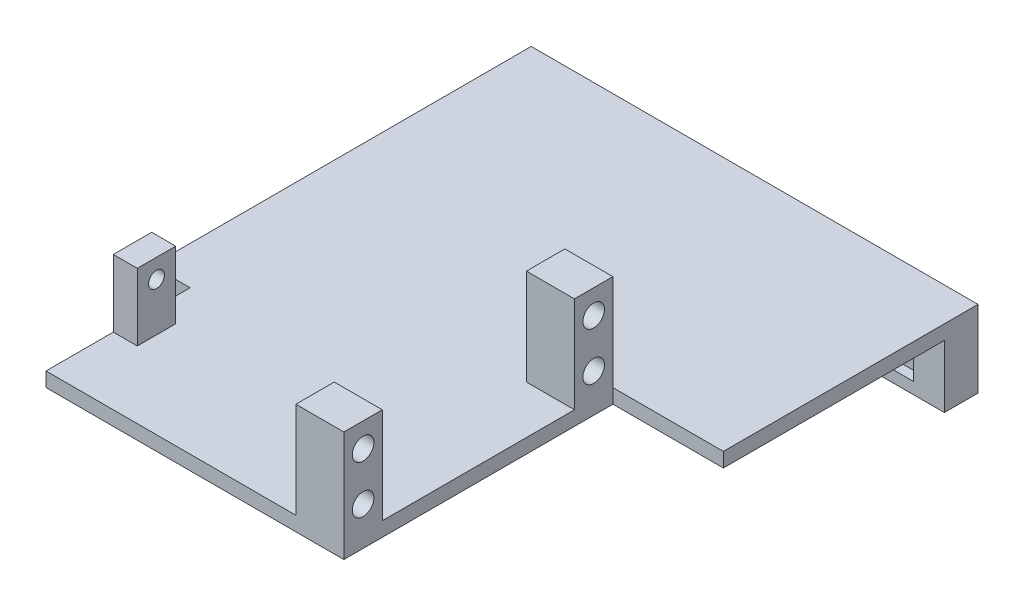
SolidWorks part; units mm, degrees
ref_plane "Plan de face" through (0, 0, 0) normal (0, 0, 1) x (1, 0, 0)
ref_plane "Plan de dessus" through (0, 0, 0) normal (0, 1, 0) x (1, 0, 0)
ref_plane "Plan de droite" through (0, 0, 0) normal (1, 0, 0) x (0, 0, -1)
sketch "Esquisse2" plane through (0, 0, 0) normal (1, 0, 0) x (0, 0, -1)
  line L0 (-24, 10) -> (-24, -10) construction
  line L1 (-24, 5) -> (24, 5) construction
  line L2 (-24, 5) -> (-24, -5) construction
  line L3 (-24, -5) -> (24, -5) construction
  line L4 (24, 5) -> (24, -5) construction
  line L5 (-24, 5) -> (24, -5) construction
  line L6 (-24, -5) -> (24, 5) construction
  line L7 (-28, 10) -> (-20, 10)
  line L8 (-28, 10) -> (-28, -10)
  line L9 (-28, -10) -> (-20, -10)
  line L10 (-20, 10) -> (-20, -10)
  line L11 (20, -10) -> (28, -10)
  line L12 (20, -10) -> (20, 10)
  line L13 (20, 10) -> (28, 10)
  line L14 (28, -10) -> (28, 10)
  line L15 (0, 0) -> (-24, 0) construction
  line L16 (24, 10) -> (24, -10) construction
  line L17 (0, 0) -> (24, 0) construction
  circle A0 centre (-24, 5) radius 2.25
  circle A1 centre (24, 5) radius 2.25
  circle A2 centre (24, -5) radius 2.25
  circle A3 centre (-24, -5) radius 2.25
  point P0 (0, 0)
  dimension "D3" = 4.5
  dimension "D1" = 10
  dimension "D2" = 48
  dimension "D4" = 20
  dimension "D5" = 8
extrude "Boss.-Extru.1" add sketch "Esquisse2" along normal blind 10
sketch "Esquisse3" plane through (0, -10, 0) normal (0, -1, 0) x (1, 0, 0)
  line L0 (10, 28) -> (0, 28) construction
  line L1 (-60, 28) -> (33, 28) construction
  line L2 (-60, 28) -> (-60, -72)
  line L3 (-60, -72) -> (33, -72)
  line L4 (33, 28) -> (33, -72) construction
  line L5 (10, 28) -> (10, -28)
  line L6 (10, -28) -> (33, -28)
  line L7 (10, 28) -> (-60, 28)
  line L8 (33, -28) -> (33, -72)
  dimension "D1" = 100
  dimension "D2" = 93
  dimension "D3" = 23
extrude "Boss.-Extru.2" add sketch "Esquisse3" along normal blind 3
sketch "Esquisse7" plane through (33, 0, 0) normal (1, 0, 0) x (0, 0, -1)
  line L0 (72, -10) -> (81, -10)
  line L1 (81, -10) -> (81, -26)
  line L2 (81, -26) -> (74, -26)
  line L3 (74, -26) -> (74, -13)
  line L4 (74, -13) -> (72, -13)
  line L5 (72, -10) -> (72, -13)
  dimension "D1" = 7
  dimension "D2" = 13
  dimension "D3" = 2
extrude "Boss.-Extru.5" add sketch "Esquisse7" against normal up to surface (93 mm away) up to face at (-60, -11.5, -22)
sketch "Esquisse8" plane through (0, -10, 0) normal (0, 1, 0) x (1, 0, 0)
  line L1 (-60, -28) -> (-52, -28)
  line L2 (-60, -28) -> (-60, 2)
  line L3 (-60, 2) -> (-52, 2)
  line L4 (-52, -28) -> (-52, 2)
  dimension "D1" = 30
  dimension "D2" = 8
extrude "Enlèv. mat.-Extru.1" cut sketch "Esquisse8" against normal up to next
sketch "Esquisse9" plane through (0, 0, -74) normal (0, 0, 1) x (1, 0, 0)
  line L0 (-13.5, -19.5) -> (-13.5, -26) construction
  line L1 (-53.6, -15.4) -> (26.6, -15.4)
  line L2 (-53.6, -15.4) -> (-53.6, -23.6)
  line L3 (-53.6, -23.6) -> (26.6, -23.6)
  line L4 (26.6, -15.4) -> (26.6, -23.6)
  line L5 (-53.6, -15.4) -> (26.6, -23.6) construction
  line L6 (-53.6, -23.6) -> (26.6, -15.4) construction
  line L7 (-60, -26) -> (33, -26) construction
  line L8 (-60, -19.5) -> (-13.5, -19.5) construction
  line L9 (-60, -26) -> (-60, -13) construction
  point P0 (-13.5, -19.5)
  dimension "D1" = 80.2
  dimension "D2" = 8.2
extrude "Enlèv. mat.-Extru.2" cut sketch "Esquisse9" against normal blind 2
sketch "Esquisse10" plane through (-52, 0, 0) normal (-1, 0, 0) x (0, 0, 1)
  line L0 (10, 0) -> (28, 0) construction
  line L1 (28, 10) -> (28, -10) construction
  line L2 (28, 0) -> (28, -10) construction
  line L3 (28, -10) -> (-2, -10) construction
  line L4 (6, -10) -> (14, -10)
  line L5 (6, -10) -> (6, 4)
  line L6 (6, 4) -> (14, 4)
  line L7 (14, -10) -> (14, 4)
  line L8 (10, 0) -> (10, 4) construction
  circle A0 centre (10, 0) radius 1.65
  dimension "D3" = 3.3
  dimension "D1" = 10
  dimension "D2" = 18
  dimension "D4" = 8
  dimension "D5" = 14
extrude "Boss.-Extru.6" add sketch "Esquisse10" against normal blind 5
